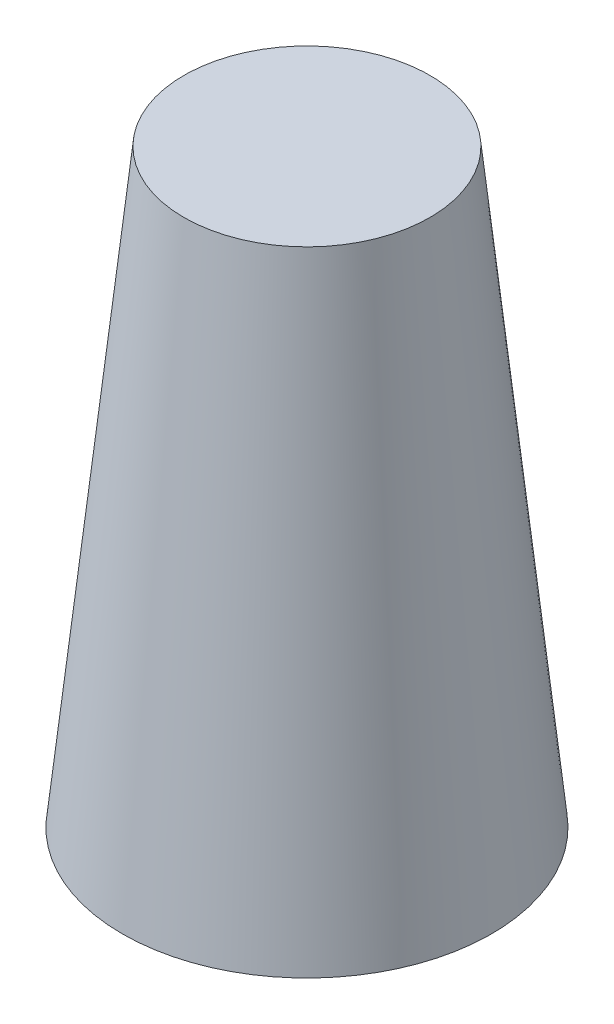
SolidWorks part; units mm, degrees
ref_plane "Front Plane" through (0, 0, 0) normal (0, 0, 1) x (1, 0, 0)
ref_plane "Top Plane" through (0, 0, 0) normal (0, 1, 0) x (1, 0, 0)
ref_plane "Right Plane" through (0, 0, 0) normal (1, 0, 0) x (0, 0, -1)
ref_axis "Axis1" through (0, 55, 0) along (0, -1, 0)
sketch "Sketch1" plane through (0, 0, 0) normal (0, 0, 1) x (1, 0, 0)
  line L0 (0, 115) -> (24, 115)
  line L1 (0, 55) -> (0, -55) construction
  line L2 (24, 115) -> (36, 0)
  line L3 (36, 0) -> (34.4919, 0)
  line L4 (34.4919, 0) -> (22.6484, 113.5)
  line L5 (22.6484, 113.5) -> (0, 113.5)
  line L6 (0, 113.5) -> (0, 115)
  point P8 (24.7793, 44.9191)
  point P10 (27.1252, 0)
  dimension "D1" = 1.5
  dimension "D2" = 36
  dimension "D3" = 24
  dimension "D4" = 1.5
  dimension "D5" = 115
revolve "Revolve1" add sketch "Sketch1" angle 360 about axis through (0, 55, 0) along (0, -1, 0)
